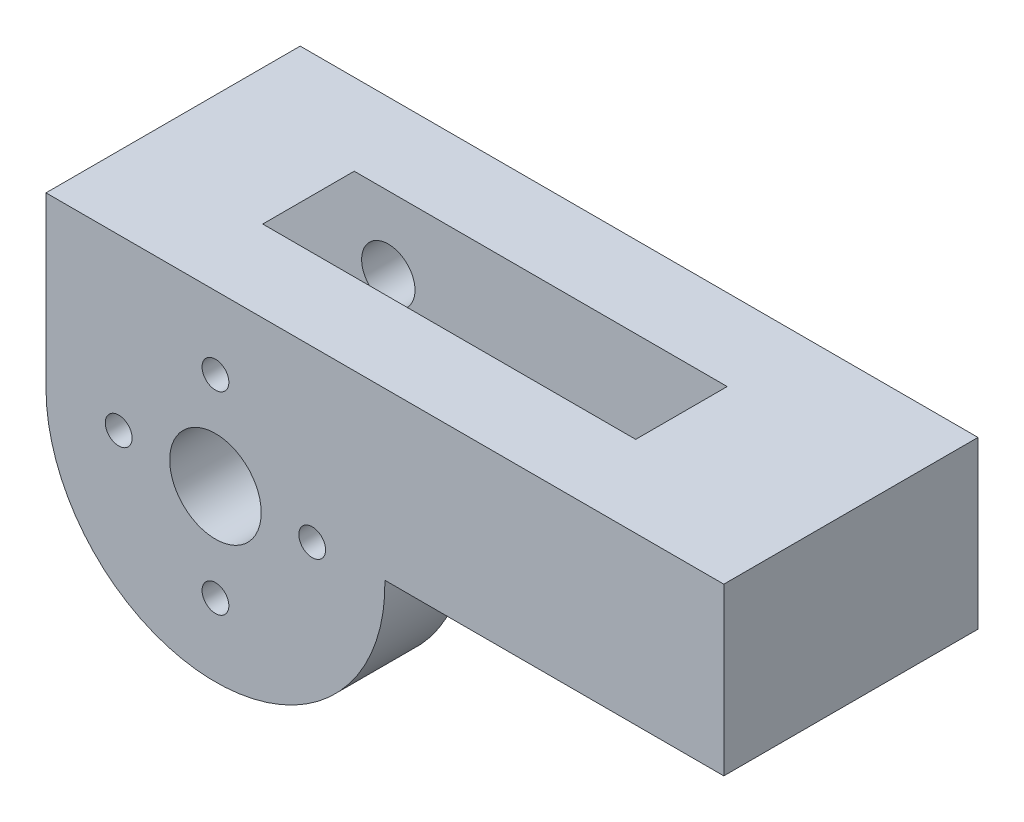
SolidWorks part; units mm, degrees
ref_plane "Front Plane" through (0, 0, 0) normal (0, 0, 1) x (1, 0, 0)
ref_plane "Top Plane" through (0, 0, 0) normal (0, 1, 0) x (1, 0, 0)
ref_plane "Right Plane" through (0, 0, 0) normal (1, 0, 0) x (0, 0, -1)
sketch "Sketch1" plane through (0, 0, 0) normal (0, 0, 1) x (1, 0, 0)
  line L0 (-12.7, 0) -> (-12.7, 12.7)
  line L5 (-12.7, 12.7) -> (38.1, 12.7)
  line L6 (38.1, 12.7) -> (38.1, 0.254)
  line L7 (38.1, 0.254) -> (12.6975, 0.254)
  arc A1 (-12.7, 0) -> (12.6975, 0.254) centre (0, 0) ccw
  circle A2 centre (0, 0) radius 3.429
  dimension "D3" = 6.858
  dimension "D1" = 12.7
  dimension "D2" = 0.254
  dimension "D4" = 38.1
  dimension "D5" = 12.7
extrude "Boss-Extrude1" add sketch "Sketch1" along normal mid plane 19.05
sketch "Sketch3" plane through (0, 0, 9.525) normal (0, 0, 1) x (1, 0, 0)
  line L2 (25.4, 12.7) -> (25.4, 0.254)
  line L3 (12.6975, 0.254) -> (38.1, 0.254) construction
  line L6 (25.4, 0.254) -> (12.9515, 0.254)
  line L14 (38.1, 0.254) -> (38.1, 12.7) construction
  line L16 (0, 12.954) -> (0, 12.7)
  line L17 (38.1, 12.7) -> (-12.7, 12.7) construction
  line L18 (0, 12.7) -> (25.4, 12.7)
  arc A2 (0, 12.954) -> (12.9515, 0.254) centre (0, 0) ccw
  dimension "D1" = 12.7
  dimension "D2" = 25.908
extrude "Cut-Extrude1" cut sketch "Sketch3" against normal mid plane 6.858 from surface at -9.525 starting at plane "Front Plane"
sketch "Sketch4" plane through (0, 0, 9.525) normal (0, 0, 1) x (1, 0, 0)
  circle A0 centre (7.25, 0) radius 1.004
  circle A1 centre (0, -7.25) radius 1.004
  circle A2 centre (-7.25, 0) radius 1.004
  circle A3 centre (0, 7.25) radius 1.004
  point P12 (0, 0)
  dimension "D3" = 2.008
  dimension "D1" = 7.25
  dimension "D2" = 4
extrude "Cut-Extrude2" cut sketch "Sketch4" against normal through all
sketch "Sketch5" plane through (0, 0, -9.525) normal (0, 0, -1) x (-1, 0, 0)
  circle A0 centre (7.25, 0) radius 2
  circle A1 centre (0, -7.25) radius 2
  circle A2 centre (-7.25, 0) radius 2
  circle A3 centre (0, 7.25) radius 2
  point P12 (0, 0)
  dimension "D2" = 4
  dimension "D1" = 4
extrude "Cut-Extrude3" cut sketch "Sketch5" against normal offset from surface (14.954 mm away) 2 up to face at (8.254, 0, 3.429) offset beyond the face yes
equation "\"tightTol\"= 0.005in"
equation "\"normTol\"= 0.01in"
equation "\"looseTol\"= 0.02in"
equation "\"D2@Sketch1\"=\"normTol\""
equation "\"D3@Sketch1\"=0.25+\"looseTol\""
equation "\"D1@Cut-Extrude1\"=\"looseTol\"+0.250000in"
equation "\"D2@Sketch3\"=1+\"looseTol\""
equation "\"D1@Sketch4\"=7.25mm"
equation "\"D3@Sketch4\"=1.5mm+\"looseTol\""
equation "\"D1@Sketch5\"=4mm"
equation "\"D1@Cut-Extrude3\"=2mm"
